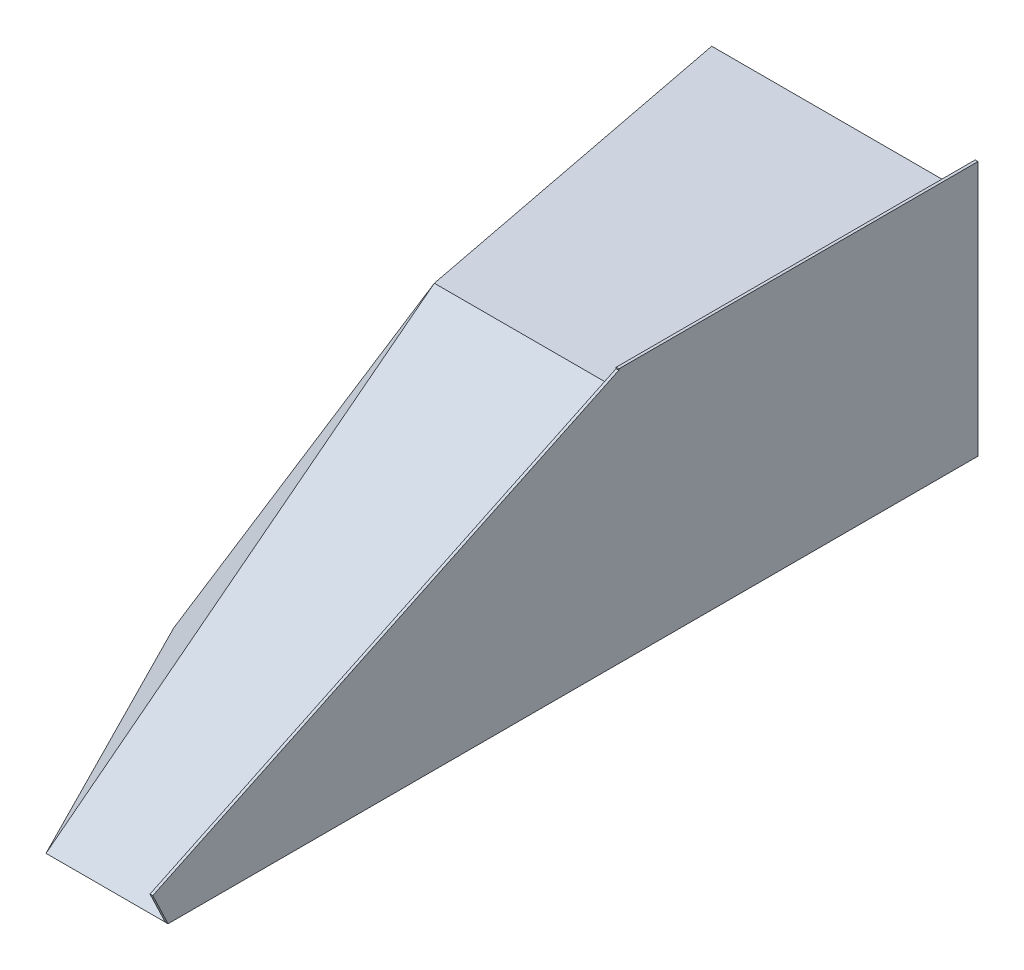
SolidWorks part; units mm, degrees
ref_plane "Front Plane" through (0, 0, 0) normal (0, 0, 1) x (1, 0, 0)
ref_plane "Top Plane" through (0, 0, 0) normal (0, 1, 0) x (1, 0, 0)
ref_plane "Right Plane" through (0, 0, 0) normal (1, 0, 0) x (0, 0, -1)
sketch "Sketch1" plane through (0, 0, 0) normal (0, 1, 0) x (1, 0, 0)
  line L0 (0, 1066.8) -> (0, 0)
  line L1 (0, 0) -> (279.4, 0)
  line L2 (279.4, 0) -> (457.2, 1066.8)
  line L3 (457.2, 1066.8) -> (0, 1066.8)
  dimension "D1" = 279.4
  dimension "D2" = 457.2
  dimension "D3" = 1066.8
extrude "Boss-Extrude1" add sketch "Sketch1" along normal blind 508
sketch "Sketch2" plane through (0, 0, 0) normal (-1, 0, 0) x (0, 0, 1)
  line L0 (0, 0) -> (-1066.8, 508)
  line L1 (-1066.8, 508) -> (-1066.8, 732.6724)
  line L2 (-1066.8, 732.6724) -> (0, 732.6724)
  line L3 (0, 732.6724) -> (0, 0)
extrude "Cut-Extrude1" cut sketch "Sketch2" against normal blind 508
sketch "Sketch3" plane through (0, 0, 0) normal (0, -1, 0) x (1, 0, 0)
  line L0 (0, -1066.8) -> (0, -1854.2)
  line L1 (0, -1854.2) -> (609.6, -1854.2)
  line L2 (609.6, -1854.2) -> (457.2, -1066.8)
  line L3 (457.2, -1066.8) -> (0, -1066.8)
  dimension "D1" = 787.4
  dimension "D2" = 609.6
extrude "Boss-Extrude2" add sketch "Sketch3" against normal blind 508
ref_point "Point1"
sketch "Sketch4" plane through (0, 0, 0) normal (0, -1, 0) x (1, 0, 0)
  line L0 (279.4, 0) -> (758.0246, -943.9298)
  line L1 (758.0246, -943.9298) -> (824.1633, -1854.2)
  line L2 (824.1633, -1854.2) -> (609.6, -1854.2)
  line L4 (609.6, -1854.2) -> (473.6054, -1854.2)
  line L5 (473.6054, -1854.2) -> (229.3242, -858.0039)
  line L6 (229.3242, -858.0039) -> (279.4, 0)
extrude "Boss-Extrude3" add sketch "Sketch4" against normal blind 635 separate body
ref_plane "Plane1" through (158.0257, 112.9593, 80.1278) normal (-0.7521, -0.5376, -0.3813) x (-0.3102, -0.2218, 0.9244)
sketch "Sketch5" plane through (158.0257, 112.9593, 80.1278) normal (-0.7521, -0.5376, -0.3813) x (-0.3102, -0.2218, 0.9244)
  line L0 (-393.6646, 703.6256) -> (953.2419, -176.9288)
  line L1 (953.2419, -176.9288) -> (-1326.8428, -923.5564)
  line L2 (-1326.8428, -923.5564) -> (-2274.7883, -628.3267)
  line L3 (-2274.7883, -628.3267) -> (-2325.5283, 172.3758)
  line L4 (-2325.5283, 172.3758) -> (-393.6646, 703.6256)
extrude "Cut-Extrude3" cut sketch "Sketch5" against normal blind 1016
ref_plane "Plane2" through (397.9401, 254.279, 77.0207) normal (0.8317, 0.5314, 0.161) x (0.1356, 0.0867, -0.987)
sketch "Sketch6" plane through (397.9401, 254.279, 77.0207) normal (0.8317, 0.5314, 0.161) x (0.1356, 0.0867, -0.987)
  line L0 (1082.533, 1261.8546) -> (2538.8005, 767.6885)
  line L1 (2538.8005, 767.6885) -> (2437.6041, -1113.0464)
  line L2 (2437.6041, -1113.0464) -> (306.9995, -1023.5801)
  line L3 (306.9995, -1023.5801) -> (1082.533, 1261.8546)
extrude "Cut-Extrude6" cut sketch "Sketch6" along normal blind 508
sketch "Sketch7" plane through (0, 0, 0) normal (0, 0.9029, 0.4299) x (1, 0, 0)
  line L0 (0, 1181.5779) -> (0, 0)
  line L1 (0, 0) -> (1197.0459, 0)
  line L2 (1197.0459, 0) -> (1543.8795, 955.9278)
  line L3 (1543.8795, 955.9278) -> (976.3528, 2301.292)
  line L4 (976.3528, 2301.292) -> (0, 1181.5779)
extrude "Cut-Extrude7" cut sketch "Sketch7" along normal blind 1016
ref_plane "Plane3" through (382.6816, 161.6328, 74.0674) normal (0.9069, 0.383, 0.1755) x (0.1617, 0.0683, -0.9845)
sketch "Sketch8" plane through (382.6816, 161.6328, 74.0674) normal (0.9069, 0.383, 0.1755) x (0.1617, 0.0683, -0.9845)
  line L0 (1197.5568, 999.1439) -> (2455.296, 323.4977)
  line L1 (2455.296, 323.4977) -> (2410.7054, -956.0431)
  line L2 (2410.7054, -956.0431) -> (776.2886, -956.0431)
  line L3 (776.2886, -956.0431) -> (430.3512, -503.2752)
  line L4 (430.3512, -503.2752) -> (1197.5568, 999.1439)
extrude "Cut-Extrude8" cut sketch "Sketch8" along normal blind 1016
sketch "Sketch9" plane through (0, 508, 0) normal (0, 1, 0) x (1, 0, 0)
  line L0 (351.5224, 2301.2259) -> (1863.402, 1800.0992)
  line L1 (1863.402, 1800.0992) -> (1313.9442, 629.1947)
  line L2 (1313.9442, 629.1947) -> (-286.9383, 375.0155)
  line L3 (-286.9383, 375.0155) -> (-444.0043, 1364.2557)
  line L4 (-444.0043, 1364.2557) -> (351.5224, 2301.2259)
extrude "Cut-Extrude9" cut sketch "Sketch9" along normal blind 1016
mirror "Mirror1" about plane through (0, 508, -1066.8) normal (1, 0, 0) of "Cut-Extrude9", "Cut-Extrude8", "Cut-Extrude7", "Cut-Extrude6", "Cut-Extrude3", "Boss-Extrude3", "Boss-Extrude2", "Cut-Extrude1", "Boss-Extrude1"
sketch "Sketch10" plane through (0, 0, 0) normal (1, 0, 0) x (0, 0, -1)
  line L0 (2306.149, 875.5358) -> (458.2361, 1137.3262)
  line L1 (458.2361, 1137.3262) -> (-514.5683, 141.1836)
  line L2 (-514.5683, 141.1836) -> (336.7011, -1596.6553)
  line L3 (336.7011, -1596.6553) -> (2036.8027, -1025.7127)
  line L4 (2036.8027, -1025.7127) -> (2740.0968, -499.6222)
  line L5 (2740.0968, -499.6222) -> (2306.149, 875.5358)
extrude "Cut-Extrude10" cut sketch "Sketch10" along normal through all
sketch "Sketch11" plane through (0, 508, 0) normal (0, 1, 0) x (1, 0, 0)
  line L0 (-609.6, 1854.2) -> (0, 1854.2) construction
  line L1 (0, 1032.0858) -> (-6.35, 1032.0858)
  line L2 (0, 1032.0858) -> (0, 1854.2)
  line L3 (0, 1854.2) -> (-6.35, 1854.2)
  line L4 (-6.35, 1032.0858) -> (-6.35, 1854.2)
  point P7 (-6.35, 1443.1429)
  dimension "D1" = 6.35
extrude "Boss-Extrude4" add sketch "Sketch11" along normal blind 76.2
sketch "Sketch12" plane through (0, 0, 0) normal (0, 0.9029, 0.4299) x (1, 0, 0)
  line L0 (-6.35, 1181.5779) -> (-457.2, 1181.5779) construction
  line L1 (0, 0) -> (-6.35, 0)
  line L2 (0, 0) -> (0, 1181.5779)
  line L3 (0, 1181.5779) -> (-6.35, 1181.5779)
  line L4 (-6.35, 0) -> (-6.35, 1181.5779)
  dimension "D1" = 6.35
extrude "Boss-Extrude5" add sketch "Sketch12" along normal blind 81.28
